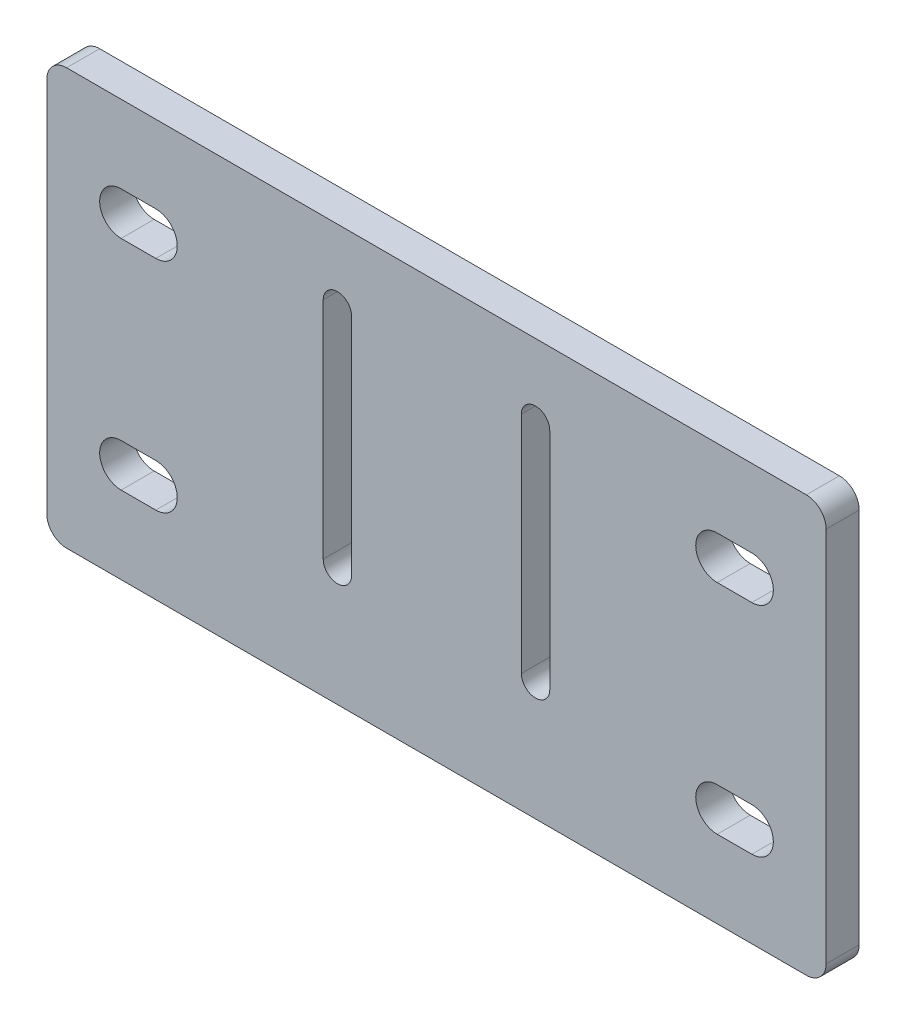
SolidWorks part; units mm, degrees
ref_plane "前视基准面" through (0, 0, 0) normal (0, 0, 1) x (1, 0, 0)
ref_plane "上视基准面" through (0, 0, 0) normal (0, 1, 0) x (1, 0, 0)
ref_plane "右视基准面" through (0, 0, 0) normal (1, 0, 0) x (0, 0, -1)
sketch "草图1" plane through (0, 0, 0) normal (0, 0, 1) x (1, 0, 0)
  line L0 (-59, -25) -> (-59, -32)
  line L1 (59, -25) -> (-59, -25) construction
  line L2 (59, -25) -> (59, 25)
  line L3 (56, 28) -> (-56, 28)
  line L4 (-59, -25) -> (-59, 25)
  line L5 (0, 28) -> (0, -25) construction
  line L6 (59, 0) -> (-59, 0) construction
  line L7 (-56, -35) -> (56, -35)
  line L8 (59, -32) -> (59, -25)
  line L9 (-49, 28) -> (-49, -35) construction
  line L10 (49, 28) -> (49, -35) construction
  line L11 (-15, -17) -> (-15, 17) construction
  line L12 (15, -17) -> (15, 17) construction
  line L13 (15, -17) -> (15, 17) construction
  line L14 (12.85, -17) -> (12.85, 17)
  line L15 (17.15, -17) -> (17.15, 17)
  line L16 (-12.85, -17) -> (-12.85, 17)
  line L17 (-17.15, -17) -> (-17.15, 17)
  arc A0 (56, -35) -> (59, -32) centre (56, -32) ccw
  arc A1 (-59, -32) -> (-56, -35) centre (-56, -32) ccw
  arc A2 (59, 25) -> (56, 28) centre (56, 25) ccw
  arc A3 (-56, 28) -> (-59, 25) centre (-56, 25) ccw
  arc A4 (12.85, -17) -> (17.15, -17) centre (15, -17) ccw
  arc A5 (17.15, 17) -> (12.85, 17) centre (15, 17) ccw
  arc A6 (-12.85, -17) -> (-17.15, -17) centre (-15, -17) cw
  arc A7 (-17.15, 17) -> (-12.85, 17) centre (-15, 17) cw
  point P0 (0, 0)
  point P17 (-59, -35)
  point P20 (59, 28)
  point P23 (-59, 28)
  point P26 (15, 0)
  point P29 (15, 0)
  point P35 (-15, 0)
  dimension "D5" = 3
  dimension "D1" = 118
  dimension "D2" = 53
  dimension "D3" = 10
  dimension "D4" = 10
  dimension "D7" = 34
  dimension "D8" = 4.3
  dimension "D9" = 41.85
extrude "凸台-拉伸1" add sketch "草图1" along normal blind 5
ref_plane "基准面1" through (0, 0, 0) normal (-1, 0, 0) x (0, 0, 1)
sketch "草图2" plane through (0, 0, 5) normal (0, 0, 1) x (1, 0, 0)
  line L0 (-51, 13) -> (-39.25, 13) construction
  line L2 (-59, 25) -> (-59, -32) construction
  line L3 (56, 28) -> (-56, 28) construction
  line L4 (-47.75, 13) -> (-42.5, 13) construction
  line L5 (-47.75, 16.25) -> (-42.5, 16.25)
  line L6 (-47.75, 9.75) -> (-42.5, 9.75)
  line L7 (-59, -3.5) -> (-17.15, -3.5) construction
  line L9 (-17.15, 17) -> (-17.15, -17) construction
  line L10 (-47.75, -20) -> (-42.5, -20) construction
  line L11 (-47.75, -23.25) -> (-42.5, -23.25)
  line L12 (-47.75, -16.75) -> (-42.5, -16.75)
  line L13 (0, 28) -> (0, -35.1544) construction
  line L14 (0, 2.75) -> (0, -2.75) construction
  line L15 (47.75, 13) -> (42.5, 13) construction
  line L16 (47.75, 16.25) -> (42.5, 16.25)
  line L17 (47.75, 9.75) -> (42.5, 9.75)
  line L18 (47.75, -20) -> (42.5, -20) construction
  line L19 (47.75, -23.25) -> (42.5, -23.25)
  line L20 (47.75, -16.75) -> (42.5, -16.75)
  arc A0 (-47.75, 16.25) -> (-47.75, 9.75) centre (-47.75, 13) ccw
  arc A1 (-42.5, 9.75) -> (-42.5, 16.25) centre (-42.5, 13) ccw
  arc A2 (-47.75, -23.25) -> (-47.75, -16.75) centre (-47.75, -20) cw
  arc A3 (-42.5, -16.75) -> (-42.5, -23.25) centre (-42.5, -20) cw
  arc A4 (47.75, 16.25) -> (47.75, 9.75) centre (47.75, 13) cw
  arc A5 (42.5, 9.75) -> (42.5, 16.25) centre (42.5, 13) cw
  arc A6 (47.75, -23.25) -> (47.75, -16.75) centre (47.75, -20) ccw
  arc A7 (42.5, -16.75) -> (42.5, -23.25) centre (42.5, -20) ccw
  point P8 (-45.125, 13)
  point P13 (-51, 13)
  point P15 (-39.25, 13)
  point P22 (-45.125, -20)
  point P34 (45.125, 13)
  point P41 (45.125, -20)
  dimension "D1" = 11.75
  dimension "D2" = 8
  dimension "D3" = 15
  dimension "D4" = 6.5
extrude "切除-拉伸1" cut sketch "草图2" against normal blind 10
